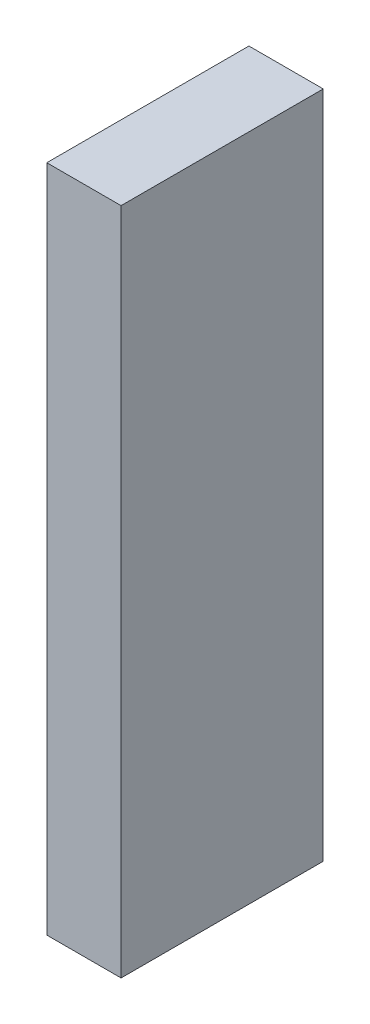
SolidWorks part; units mm, degrees
material "POLYURETHANE (11671)"
ref_plane "Front Plane" through (0, 0, 0) normal (0, 0, 1) x (1, 0, 0)
ref_plane "Top Plane" through (0, 0, 0) normal (0, 1, 0) x (1, 0, 0)
ref_plane "Right Plane" through (0, 0, 0) normal (1, 0, 0) x (0, 0, -1)
sketch "Sketch1" plane through (0, 0, 0) normal (1, 0, 0) x (0, 0, -1)
  line L1 (-4.318, -14.2875) -> (4.318, -14.2875)
  line L2 (-4.318, -14.2875) -> (-4.318, 14.2875)
  line L3 (-4.318, 14.2875) -> (4.318, 14.2875)
  line L4 (4.318, -14.2875) -> (4.318, 14.2875)
  line L5 (-4.318, -14.2875) -> (4.318, 14.2875) construction
  line L6 (-4.318, 14.2875) -> (4.318, -14.2875) construction
  point P0 (0, 0)
  dimension "D1" = 8.636
  dimension "D2" = 28.575
extrude "Boss-Extrude1" add sketch "Sketch1" along normal blind 3.175
